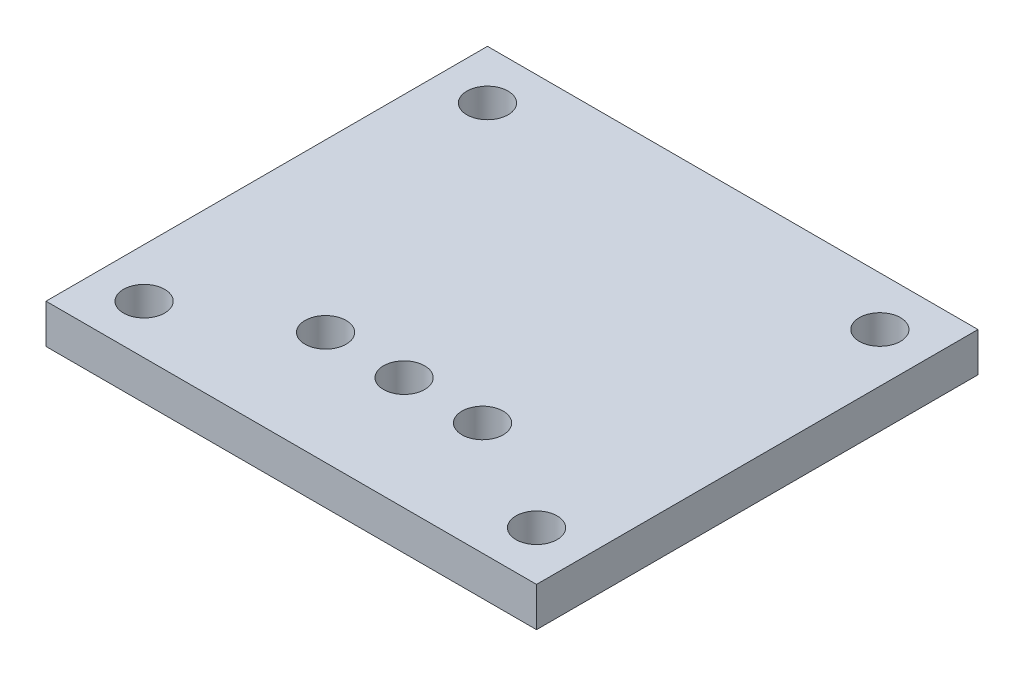
SolidWorks part; units mm, degrees
ref_plane "前视基准面" through (0, 0, 0) normal (0, 0, 1) x (1, 0, 0)
ref_plane "上视基准面" through (0, 0, 0) normal (0, 1, 0) x (1, 0, 0)
ref_plane "右视基准面" through (0, 0, 0) normal (1, 0, 0) x (0, 0, -1)
sketch "草图1" plane through (0, 0, 0) normal (0, 1, 0) x (1, 0, 0)
  line L1 (-25, 22.5) -> (25, 22.5)
  line L2 (-25, 22.5) -> (-25, -22.5)
  line L3 (-25, -22.5) -> (25, -22.5)
  line L4 (25, 22.5) -> (25, -22.5)
  line L5 (-25, 22.5) -> (25, -22.5) construction
  line L6 (-25, -22.5) -> (25, 22.5) construction
  point P0 (0, 0)
  dimension "D1" = 50
  dimension "D2" = 45
extrude "凸台-拉伸1" add sketch "草图1" along normal blind 4
sketch "草图2" plane through (0, 4, 0) normal (0, 1, 0) x (1, 0, 0)
  line L0 (-8, -11) -> (8, -11) construction
  line L1 (0, 0) -> (0, -11) construction
  circle A0 centre (0, -11) radius 2.1
  circle A1 centre (8, -11) radius 2.1
  circle A2 centre (-8, -11) radius 2.1
  point P4 (0, -11)
  dimension "D1" = 4.2
  dimension "D2" = 16
  dimension "D3" = 11
extrude "切除-拉伸1" cut sketch "草图2" against normal through all
sketch "草图5" plane through (0, 0, 0) normal (0, -1, 0) x (-1, 0, 0)
  line L1 (20, 17.5) -> (-20, 17.5) construction
  line L2 (20, 17.5) -> (20, -17.5) construction
  line L3 (20, -17.5) -> (-20, -17.5) construction
  line L4 (-20, 17.5) -> (-20, -17.5) construction
  line L5 (20, 17.5) -> (-20, -17.5) construction
  line L6 (20, -17.5) -> (-20, 17.5) construction
  circle A0 centre (20, -17.5) radius 2.1
  circle A1 centre (20, 17.5) radius 2.1
  circle A2 centre (-20, 17.5) radius 2.1
  circle A3 centre (-20, -17.5) radius 2.1
  point P0 (0, 0)
  dimension "D3" = 4.2
  dimension "D1" = 40
  dimension "D2" = 35
extrude "切除-拉伸4" cut sketch "草图5" against normal through all
